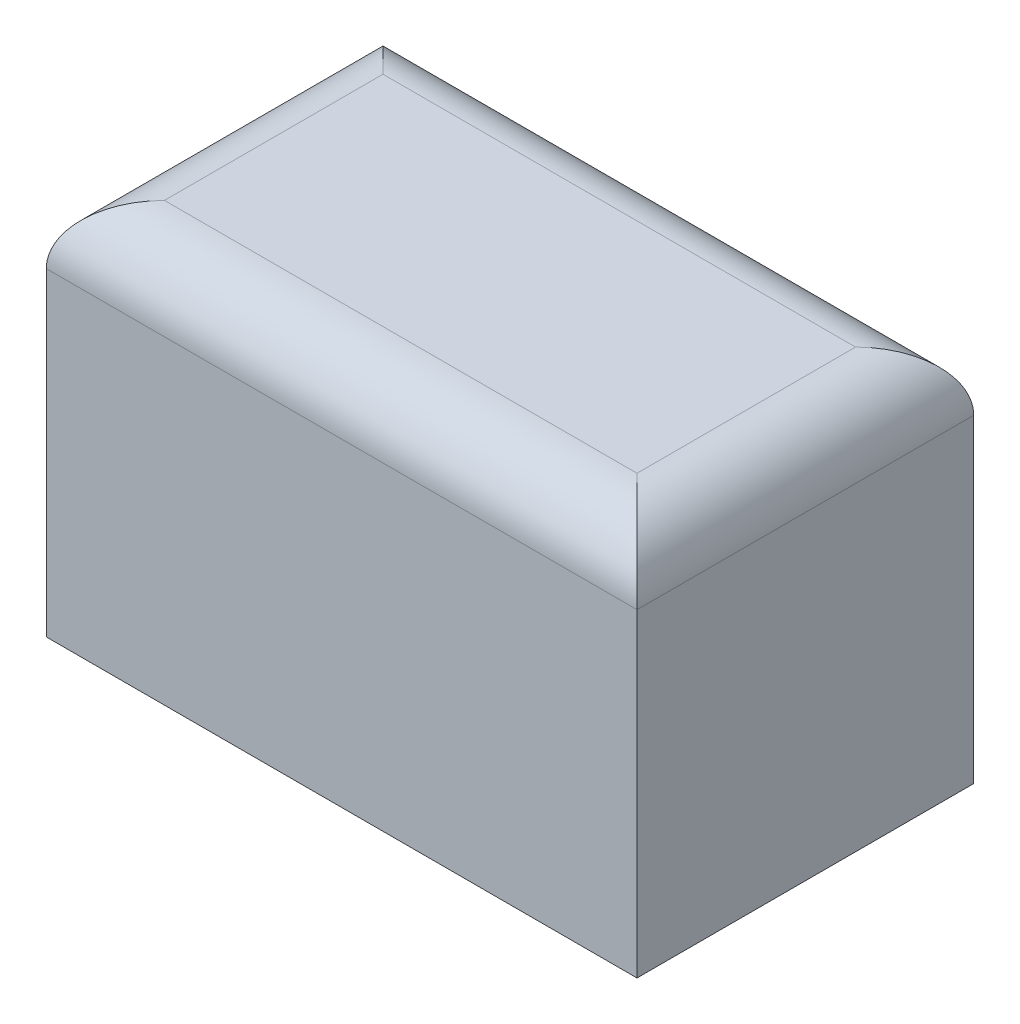
SolidWorks part; units mm, degrees
ref_plane "Front Plane" through (0, 0, 0) normal (0, 0, 1) x (1, 0, 0)
ref_plane "Top Plane" through (0, 0, 0) normal (0, 1, 0) x (1, 0, 0)
ref_plane "Right Plane" through (0, 0, 0) normal (1, 0, 0) x (0, 0, -1)
sketch "Sketch1" plane through (0, 0, 0) normal (0, 1, 0) x (1, 0, 0)
  line L1 (-5, -2.85) -> (5, -2.85)
  line L2 (-5, -2.85) -> (-5, 2.85)
  line L3 (-5, 2.85) -> (5, 2.85)
  line L4 (5, -2.85) -> (5, 2.85)
  line L5 (-5, -2.85) -> (5, 2.85) construction
  line L6 (-5, 2.85) -> (5, -2.85) construction
  point P0 (0, 0)
  dimension "D1" = 10
  dimension "D2" = 5.7
extrude "Boss-Extrude1" add sketch "Sketch1" along normal blind 6.4
fillet "Fillet1" radius 1 4 edges at (-5, 6.4, 0) (0, 6.4, -2.85) (5, 6.4, 0) (0, 6.4, 2.85)
